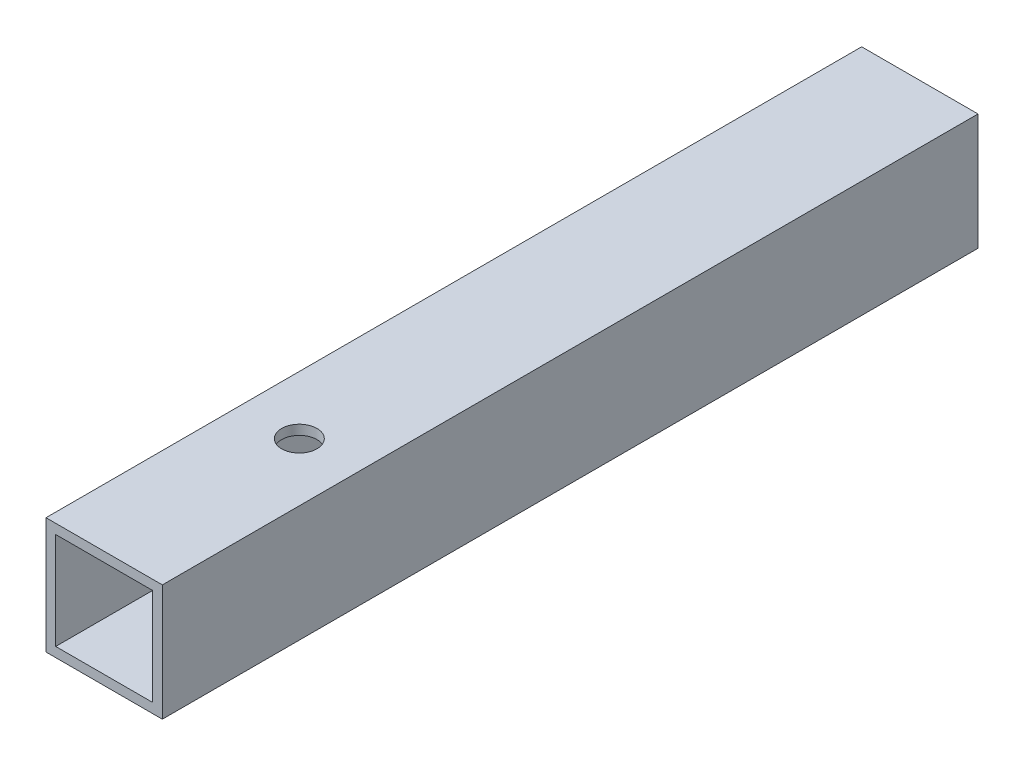
SolidWorks part; units mm, degrees
ref_plane "Front Plane" through (0, 0, 0) normal (0, 0, 1) x (1, 0, 0)
ref_plane "Top Plane" through (0, 0, 0) normal (0, 1, 0) x (1, 0, 0)
ref_plane "Right Plane" through (0, 0, 0) normal (1, 0, 0) x (0, 0, -1)
sketch "Sketch1" plane through (0, 0, 0) normal (0, 0, 1) x (0, -1, 0)
  line L1 (-9.525, 9.525) -> (9.525, 9.525)
  line L2 (-9.525, 9.525) -> (-9.525, -9.525)
  line L3 (-9.525, -9.525) -> (9.525, -9.525)
  line L4 (9.525, 9.525) -> (9.525, -9.525)
  line L5 (-9.525, 9.525) -> (9.525, -9.525) construction
  line L6 (-9.525, -9.525) -> (9.525, 9.525) construction
  line L7 (-7.9375, 7.9375) -> (7.9375, 7.9375)
  line L8 (-7.9375, 7.9375) -> (-7.9375, -7.9375)
  line L9 (-7.9375, -7.9375) -> (7.9375, -7.9375)
  line L10 (7.9375, 7.9375) -> (7.9375, -7.9375)
  line L11 (-7.9375, 7.9375) -> (7.9375, -7.9375) construction
  line L12 (-7.9375, -7.9375) -> (7.9375, 7.9375) construction
  point P0 (0, 0)
  point P5 (0, 0)
  dimension "D1" = 15.875
  dimension "D2" = 19.05
extrude "Boss-Extrude1" add sketch "Sketch1" along normal mid plane 133.5532
sketch "Sketch2" plane through (0, 9.525, 0) normal (0, 1, 0) x (1, 0, 0)
  line L0 (0, -66.7766) -> (0, -34.8234) construction
  line L1 (9.525, -66.7766) -> (-9.525, -66.7766) construction
  line L2 (9.525, 66.7766) -> (-9.525, 66.7766) construction
  circle A0 centre (0, -34.8234) radius 2.8956
  point P8 (0, 66.7766)
  dimension "D2" = 5.7912
  dimension "D1" = 101.6
extrude "BasePlateMountHole" cut sketch "Sketch2" against normal through all
sketch "Sketch3" plane through (-9.525, 0, 0) normal (-1, 0, 0) x (0, 0, 1)
  line L5 (66.7766, -45.2708) -> (-412.75, -45.2708) construction
  line L6 (3.3782, 0) -> (-412.75, 0) construction
  circle A0 centre (3.3782, 0) radius 4.7625
  point P2 (0, 0)
  point P11 (0, 0)
  point P12 (0, 0)
  point P13 (66.7766, -45.2708)
  dimension "D1" = 9.525
  dimension "D5" = 479.5266
  dimension "D6" = 416.1282
extrude "Cut-Extrude1" cut sketch "Sketch3" against normal up to next
equation "\"Height\"= 32in"
equation "\"Width\"= 23in"
equation "\"Depth\"= 20in"
equation "\"Plexi\"= .121in"
equation "\"MagnetThickness\"= 0.125in"
equation "\"MagnetDiameter\"= 12mm"
equation "\"DoorPlexi\" = \"Plexi\""
equation "\"BasePlateThickness\" = 0.5in"
equation "\"BasePlateWidth\" = \"Width\"+\"EBWidth\"-2*\"Plexi\""
equation "\"BasePlateDepth\" = \"TopBarDepth\"+2*\"CornerCube\""
equation "\"Boxsize\" = .75in"
equation "\"Boxinner\" = .625in"
equation "\"CornerCube\" = 0.75in"
equation "\"FingerLength\" = 1.125in"
equation "\"FingerWidth\" = .625in"
equation "\"Cutwidth\"= .016in"
equation "\"Earsize\"= 1in + \"Cutwidth\" /2"
equation "\"Slotsize\" = 1in - \"CutWidth\" / 2"
equation "\"InnerWidth\" = \"Width\" - 2* \"Plexi\""
equation "\"InnerHeight\" = \"Height\" -2 * \"Plexi\""
equation "\"InnerDepth\" = \"Depth\" - 2*\"Plexi\""
equation "\"RearNumHoles\" = 4"
equation "\"RearHolesBorder\" = 2.25"
equation "\"RearHoleSpacing\" = (\"Width\" - 2*\"RearHolesBorder\") / (\"RearNumHoles\"-1)"
equation "\"RearBarLength\" = (\"InnerWidth\"-2*\"CornerCube\")"
equation "\"RearTopNumHoles\" = 4"
equation "\"RearTopHolesBorder\" = 3.1"
equation "\"RearTopHolesSpacing\" = (\"Width\" - 2*\"RearTopHolesBorder\") / (\"RearTopNumHoles\"-1)"
equation "\"SideTopNumHoles\" = 4"
equation "\"SideTopHoleOffset\"=\"CornerCube\"+\"FingerLength\"+\"Plexi\"+.5"
equation "\"SideHorizNumHoles\" = 4"
equation "\"SideHorizHoleBorder\" = 1.50"
equation "\"SideVertBarLength\"=\"Height\"-\"BasePlateThickness\"-2*\"CornerCube\"-\"Plexi\""
equation "\"SideVertNumHoles\" = 4"
equation "\"SideVertHolesBorder\" = \"CornerCube\"+\"FingerLength\"+1.50"
equation "\"SideVertHoleSpacing\" = (\"InnerHeight\" - 2*\"SideVertHolesBorder\") / (\"SideVertNumHoles\"-1)"
equation "\"RearSideVertNumHoles\" = 4"
equation "\"RearSideVertHolesBorder\" = 2.4"
equation "\"RearSideVertHoleSpacing\" = (\"InnerHeight\" - 2*\"RearSideVertHolesBorder\") / (\"RearSideVertNumHoles\"-1)"
equation "\"RivetDia\" = .228in"
equation "\"SlotDepth\" = \"Plexi\" + 0.75in + .005in"
equation "\"SideSlotWidth\"   = \"Plexi\"+.005in"
equation "\"SidePanelVertSpacing\" = (\"Height\"-2*(1.75-\"Plexi\")) / 5"
equation "\"BottomPanelSideHoleSpacing\" = (\"InnerDepth\"-2*(1.75-\"Plexi\")) / 4"
equation "\"FrontDoorGap\" = .1in"
equation "\"TopDepth\" = \"Depth\"-\"DoorPlexi\"-\"FrontDoorGap\""
equation "\"TopBarDepth\" = \"Depth\"-\"DoorPlexi\"-\"Plexi\"-2*\"MagnetThickness\"-2*\"CornerCube\""
equation "\"CoolerDepth\" = 12in"
equation "\"D1@Boss-Extrude1\"=\"ShelfBarDepth\""
equation "\"SideTopHoleSpacing\" = (\"TopBarDepth\"-2*\"SideTopHoleOffset\") / (\"SideTopNumHoles\"-1)"
equation "\"SideHorizHoleSpacing\" = (\"TopBarDepth\"-2*\"SideHorizHoleBorder\") / (\"SideHorizNumHoles\"-1)"
equation "\"ShelfDepth\" = \"TopBarDepth\"+\"CornerCube\"-\"CoolerDepth\""
equation "\"BoxsizeHalf\" = \"Boxsize\"/2"
equation "\"ShelfBarDepth\"=\"ShelfDepth\"-2*\"CornerCube\""
equation "\"ShelfWidth\" = \"EBWidth\"-\"ShelfGap\""
equation "\"ShelfBarWidth\" = \"EBWidth\"-\"Boxsize\""
equation "\"ShelfGap\" = 0.5in"
equation "\"ShelfBarWidthShort\" = \"ShelfBarWidth\"-\"Boxsize\"-\"ShelfGap\""
equation "\"IntakeWidth\"=4in"
equation "\"IntakeHeight\"=2in"
equation "\"ExhaustWidth\"=4in"
equation "\"ExhaustHeight\"=2in"
equation "\"VentSpacing\"=7in"
equation "\"AngleBracketLength\"=20mm"
equation "\"AngleBracketWidth\"=.5in"
equation "\"AngleBracketThickness\"=.125in"
equation "\"AngleBracketHolePos\"=15mm"
equation "\"AngleBracketHoleDia\"=\"Rivet3_16Dia\""
equation "\"ShelfBarAngleHole\"=\"ShelfGap\"+\"Boxsize\"+\"AngleBracketHolePosShort\""
equation "\"EBWidth\" = 9in"
equation "\"ComponentMountDia\"=0.1770"
equation "\"ShelfThickness\" = .1250in"
equation "\"BinderPostDia\" = .228in"
equation "\"ShelfHeight1\" = 13in"
equation "\"ShelfHeight2\" = 24in"
equation "\"VentVertLocation\"=12.75in"
equation "\"PSBracketThickness\" = .0641in"
equation "\"D2@Sketch2\"=\"BinderPostDia\""
equation "\"EBForwardMountOffset\" = 4.0in"
equation "\"EBForwardMount\" = 2*\"Boxsize\"+\"CoolerDepth\"+\"EBForwardMountOffset\""
equation "\"D1@Sketch2\"=\"EBForwardMountOffset\""
equation "\"D5@Sketch3\" = \"Plexi\" + \"CornerCube\" * 2 + \"CoolerDepth\" + \"ShelfBarDepth\""
equation "\"D6@Sketch3\"=\"Plexi\"+\"Boxsize\"+\"SideTopHoleOffset\"+\"SideTopHoleSpacing\"*3"
